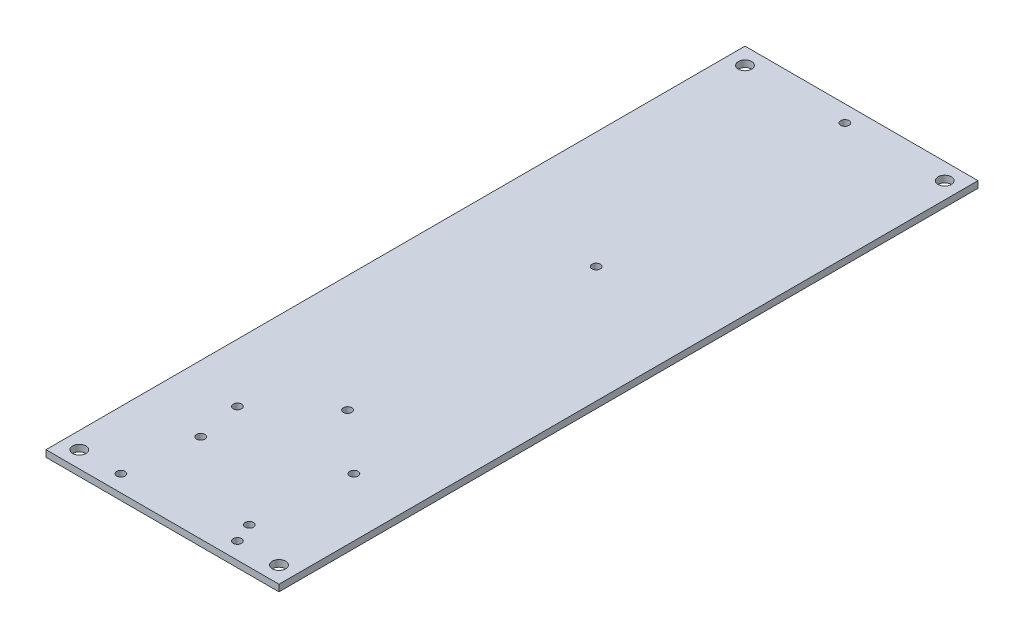
SolidWorks part; units mm, degrees
ref_plane "Front Plane" through (0, 0, 0) normal (0, 0, 1) x (1, 0, 0)
ref_plane "Top Plane" through (0, 0, 0) normal (0, 1, 0) x (1, 0, 0)
ref_plane "Right Plane" through (0, 0, 0) normal (1, 0, 0) x (0, 0, -1)
sketch "Sketch1" plane through (0, 0, 0) normal (0, 1, 0) x (1, 0, 0)
  line L1 (0, 0) -> (70, 0)
  line L2 (0, 0) -> (0, 210)
  line L3 (0, 210) -> (70, 210)
  line L4 (70, 0) -> (70, 210)
  dimension "D1" = 210
  dimension "D2" = 70
extrude "Boss-Extrude1" add sketch "Sketch1" along normal blind 2
sketch "Sketch2" plane through (0, 2, 0) normal (0, 1, 0) x (1, 0, 0)
  line L0 (70, 210) -> (0, 210) construction
  line L1 (0, 210) -> (0, 0) construction
  line L2 (35, 210) -> (35, 0) construction
  line L3 (0, 0) -> (70, 0) construction
  line L4 (0, 105) -> (70, 105) construction
  line L5 (70, 0) -> (70, 210) construction
  circle A0 centre (5, 205) radius 2
  circle A1 centre (65, 205) radius 2
  circle A2 centre (65, 5) radius 2
  circle A3 centre (5, 5) radius 2
  dimension "D1" = 5
  dimension "D3" = 4
  dimension "D2" = 5
extrude "Cut-Extrude1" cut sketch "Sketch2" against normal through all
hole_wizard "Tap Drill for M3 Tap1" positions "Sketch6" profile "Sketch7" hole size "M3" standard "ISO" end condition through all
sketch "Sketch6" plane through (0, 2, 0) normal (0, 1, 0) x (1, 0, 0)
  line L0 (35, 210) -> (35, 0) construction
  line L1 (70, 210) -> (0, 210) construction
  line L2 (0, 0) -> (70, 0) construction
  point P0 (35, 205)
  point P2 (35, 130.3)
  point P4 (35, 55.6)
  dimension "D1" = 5
  dimension "D2" = 74.7
  dimension "D3" = 74.7
sketch "Sketch7" plane through (35, 2, -205) normal (1, 0, 0) x (0, 0, 1)
  line L0 (0, 0) -> (0, 2)
  line L1 (0, 2) -> (1.25, 2)
  line L2 (1.25, 2) -> (1.25, 0)
  line L5 (1.25, 0) -> (0, 0)
  line L11 (0, -6.35) -> (0, 107.95) construction
  dimension "Thru Hole Dia." = 2.5
  dimension "Thru Hole Depth" = 2
hole_wizard "Tap Drill for M3 Tap2" positions "Sketch8" profile "Sketch9" hole size "M3" standard "ISO" end condition through all
sketch "Sketch8" plane through (0, 2, 0) normal (0, 1, 0) x (1, 0, 0)
  line L0 (0, 40) -> (70, 40) construction
  line L1 (0, 210) -> (0, 0) construction
  line L2 (70, 0) -> (70, 210) construction
  line L4 (0, 5) -> (70, 5) construction
  line L5 (17.5, 54.8415) -> (17.5, 0) construction
  line L6 (0, 0) -> (70, 0) construction
  line L8 (52.5, 58.9257) -> (52.5, 0) construction
  line L10 (35, 0) -> (35, 63.1187) construction
  point P0 (52.5, 5)
  point P2 (17.5, 5)
  point P4 (17.5, 40)
  point P6 (52.5, 40)
  dimension "D1" = 35
  dimension "D2" = 35
  dimension "D3" = 5
  dimension "D4" = 17.5
sketch "Sketch9" plane through (52.5, 2, -5) normal (1, 0, 0) x (0, 0, 1)
  line L0 (0, 0) -> (0, 2)
  line L1 (0, 2) -> (1.25, 2)
  line L2 (1.25, 2) -> (1.25, 0)
  line L5 (1.25, 0) -> (0, 0)
  line L11 (0, -6.35) -> (0, 107.95) construction
  dimension "Thru Hole Dia." = 2.5
  dimension "Thru Hole Depth" = 2
hole_wizard "Tap Drill for M3 Tap3" positions "Sketch11" profile "Sketch12" hole size "M3" standard "ISO" end condition through all
sketch "Sketch11" plane through (0, 2, 0) normal (0, 1, 0) x (1, 0, 0)
  line L0 (35, 0) -> (35, 48.6803) construction
  line L1 (0, 0) -> (70, 0) construction
  point P0 (19.9, 26.6)
  point P2 (50.1, 11)
  dimension "D1" = 15.6
  dimension "D2" = 30.2
  dimension "D3" = 15.1
  dimension "D4" = 11
sketch "Sketch12" plane through (19.9, 2, -26.6) normal (1, 0, 0) x (0, 0, 1)
  line L0 (0, 0) -> (0, 2)
  line L1 (0, 2) -> (1.25, 2)
  line L2 (1.25, 2) -> (1.25, 0)
  line L5 (1.25, 0) -> (0, 0)
  line L11 (0, -6.35) -> (0, 107.95) construction
  dimension "Thru Hole Dia." = 2.5
  dimension "Thru Hole Depth" = 2
